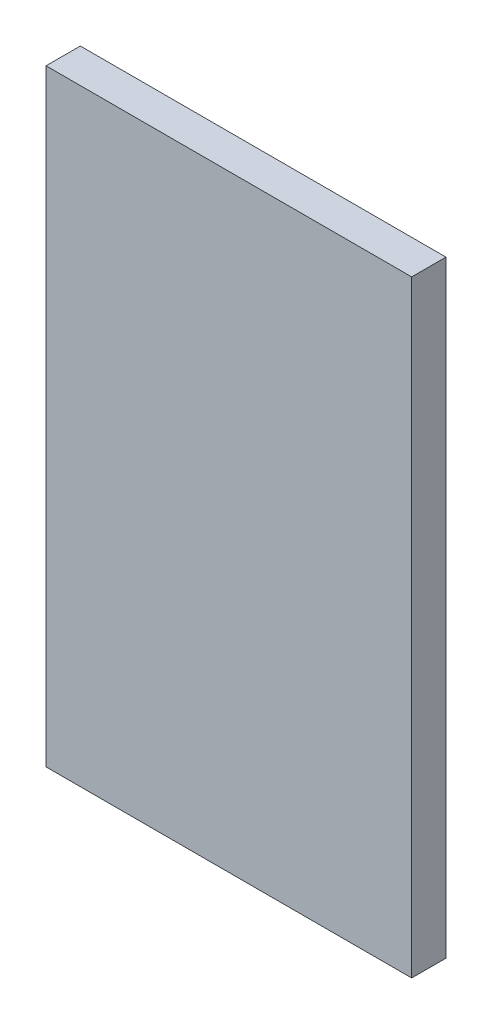
SolidWorks part; units mm, degrees
ref_plane "Front Plane" through (0, 0, 0) normal (0, 0, 1) x (1, 0, 0)
ref_plane "Top Plane" through (0, 0, 0) normal (0, 1, 0) x (1, 0, 0)
ref_plane "Right Plane" through (0, 0, 0) normal (1, 0, 0) x (0, 0, -1)
sketch "Sketch1" plane through (0, 0, 0) normal (0, 0, 1) x (1, 0, 0)
  line L1 (0, 0) -> (27.1, 0)
  line L2 (0, 0) -> (0, 45)
  line L3 (0, 45) -> (27.1, 45)
  line L4 (27.1, 0) -> (27.1, 45)
  dimension "D1" = 27.1
  dimension "D2" = 45
extrude "Boss-Extrude1" add sketch "Sketch1" along normal blind 2.54
